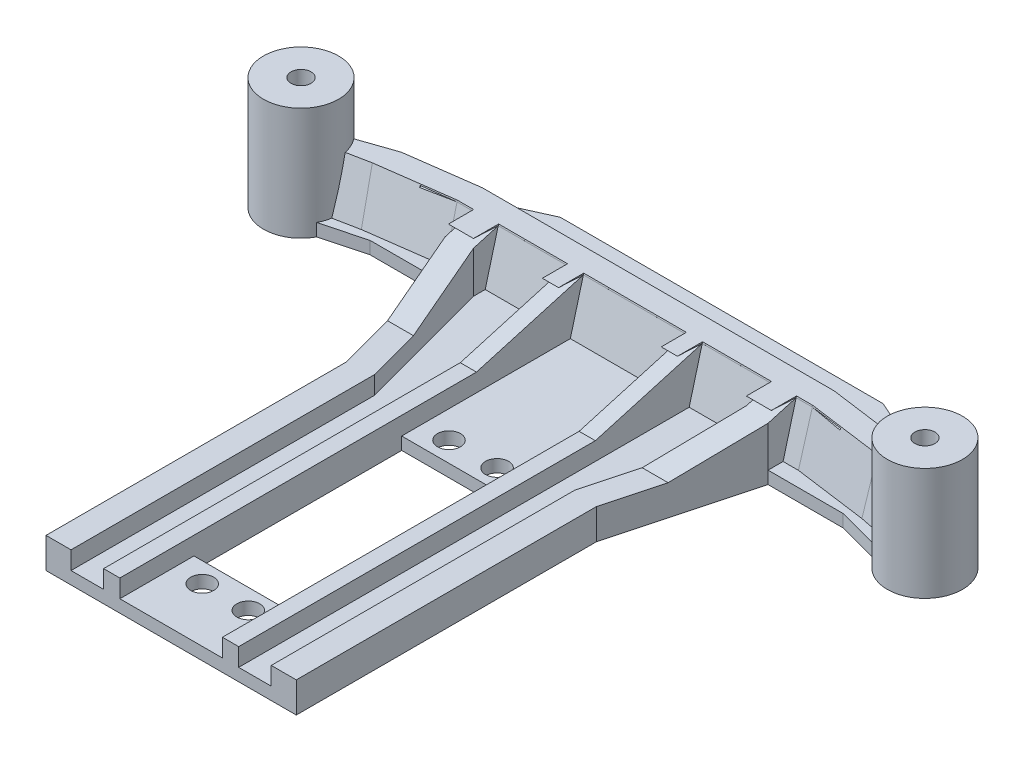
SolidWorks part; units mm, degrees
ref_plane "Front Plane" through (0, 0, 0) normal (0, 0, 1) x (1, 0, 0)
ref_plane "Top Plane" through (0, 0, 0) normal (0, 1, 0) x (1, 0, 0)
ref_plane "Right Plane" through (0, 0, 0) normal (1, 0, 0) x (0, 0, -1)
sketch "Sketch1" plane through (0, 0, 0) normal (0, 1, 0) x (1, 0, 0)
  line L0 (-25, 30) -> (-32.2561, 57)
  line L2 (-25, 30) -> (-25, -30)
  line L3 (-25, -30) -> (25, -30)
  line L4 (25, 30) -> (25, -30)
  line L5 (-25, 30) -> (25, -30) construction
  line L6 (-25, -30) -> (25, 30) construction
  line L7 (-32.2561, 57) -> (-47.2561, 57)
  line L8 (-47.2561, 57) -> (-66, 52)
  line L9 (-66, 52) -> (-66, 62)
  line L10 (-66, 62) -> (-50, 72)
  line L11 (-50, 72) -> (-32.2561, 80)
  line L12 (-32.2561, 80) -> (32.2561, 80)
  line L13 (32.2561, 80) -> (50, 72)
  line L14 (50, 72) -> (66, 62)
  line L15 (66, 62) -> (66, 52)
  line L16 (66, 52) -> (47.2561, 57)
  line L17 (47.2561, 57) -> (32.2561, 57)
  line L18 (32.2561, 57) -> (25, 30)
  line L19 (-32.2561, 57) -> (32.2561, 57) construction
  line L20 (-66, 52) -> (66, 52) construction
  line L21 (-66, 62) -> (66, 62) construction
  line L22 (-50, 72) -> (50, 72) construction
  line L23 (0, 80) -> (0, -30) construction
  line L24 (-25, 30) -> (25, 30) construction
  point P0 (0, 0)
  point P20 (0, 72)
  point P21 (0, 62)
  point P22 (0, 57)
  point P23 (-32.2561, 57)
  dimension "D1" = 50
  dimension "D2" = 60
  dimension "D3" = 50
  dimension "D4" = 27
  dimension "D5" = 15
  dimension "D6" = 15
  dimension "D7" = 5
  dimension "D8" = 5
  dimension "D9" = 10
  dimension "D10" = 100
  dimension "D11" = 132
extrude "Boss-Extrude1" add sketch "Sketch1" along normal blind 2.5
sketch "Sketch2" plane through (0, 2.5, 0) normal (0, 1, 0) x (1, 0, 0)
  line L0 (0, 0) -> (0, 5.5599) construction
  line L1 (-10.25, 26.3099) -> (10.25, 26.3099)
  line L2 (-10.25, 26.3099) -> (-10.25, -15.1901)
  line L3 (-10.25, -15.1901) -> (10.25, -15.1901)
  line L4 (10.25, 26.3099) -> (10.25, -15.1901)
  line L5 (-10.25, 26.3099) -> (10.25, -15.1901) construction
  line L6 (-10.25, -15.1901) -> (10.25, 26.3099) construction
  point P0 (0, 5.5599)
  dimension "D1" = 41.5
  dimension "D2" = 20.5
extrude "Cut-Extrude1" cut sketch "Sketch2" against normal through all
sketch "Sketch8" plane through (0, 2.5, 0) normal (0, 1, 0) x (1, 0, 0)
  line L0 (10.25, 26.3099) -> (-10.25, 26.3099) construction
  line L1 (4.8, 30.3099) -> (-4.8, 30.3099) construction
  line L2 (4.6, -19.1901) -> (-4.6, -19.1901) construction
  line L3 (0, -19.1901) -> (0, 0) construction
  line L4 (-10.25, -15.1901) -> (10.25, -15.1901) construction
  circle A0 centre (-4.8, 30.3099) radius 2.3
  circle A1 centre (4.8, 30.3099) radius 2.3
  circle A2 centre (-4.6, -19.1901) radius 2.3
  circle A3 centre (4.6, -19.1901) radius 2.3
  dimension "D4" = 4.6
  dimension "D5" = 4.6
  dimension "D1" = 4.8
  dimension "D2" = 4.8
  dimension "D3" = 4
  dimension "D6" = 9.2
  dimension "D7" = 4
extrude "Cut-Extrude2" cut sketch "Sketch8" against normal through all
sketch "Sketch9" plane through (0, 2.5, 0) normal (0, 1, 0) x (1, 0, 0)
  line L0 (-65, 62.845) -> (-50, 68)
  line L1 (-50, 68) -> (-35.3199, 70)
  line L2 (-35.3199, 70) -> (35.3199, 70)
  line L3 (35.3199, 70) -> (50, 68)
  line L4 (50, 68) -> (65, 62.845)
  line L5 (65, 62.845) -> (65, 55)
  line L6 (65, 55) -> (50, 58)
  line L7 (50, 58) -> (35.3199, 60)
  line L8 (35.3199, 60) -> (-35.3199, 60)
  line L9 (-35.3199, 60) -> (-50, 58)
  line L10 (-50, 58) -> (-65, 55)
  line L11 (-65, 55) -> (-65, 62.845)
  line L12 (-50, 58) -> (50, 58) construction
  line L13 (-50, 68) -> (50, 68) construction
  line L14 (0, 70) -> (0, 0) construction
  line L15 (-65, 55) -> (65, 55) construction
  line L16 (-35.3199, 70) -> (-35.3199, 60) construction
  line L17 (-50, 68) -> (-50, 58) construction
  line L18 (35.3199, 70) -> (35.3199, 60) construction
  line L19 (50, 68) -> (50, 58) construction
  line L20 (-65, 62.845) -> (65, 62.845) construction
  point P15 (0, 68)
  point P16 (0, 60)
  point P17 (0, 55)
  dimension "D1" = 130
  dimension "D2" = 60
  dimension "D3" = 55
  dimension "D4" = 58
  dimension "D5" = 70
  dimension "D6" = 100
extrude "Boss-Extrude2" add sketch "Sketch9" along normal blind 10 draft 15
sketch "Sketch10" plane through (0, 2.5, 0) normal (0, 1, 0) x (1, 0, 0)
  circle A0 centre (-62.3205, 58.2685) radius 7.5
  circle A1 centre (62.3205, 58.2685) radius 7.5
  dimension "D1" = 15
  dimension "D2" = 15
extrude "Boss-Extrude3" add sketch "Sketch10" along normal blind 20 and the other way blind 2.5
sketch "Sketch11" plane through (0, 22.5, 0) normal (0, 1, 0) x (1, 0, 0)
  circle A0 centre (-62.3205, 58.2685) radius 2
  circle A1 centre (62.3205, 58.2685) radius 2
extrude "Cut-Extrude3" cut sketch "Sketch11" against normal through all
sketch "Sketch12" plane through (0, 2.5, 0) normal (0, 1, 0) x (1, 0, 0)
  line L0 (-25, -30) -> (-25, 30)
  line L1 (-25, 30) -> (-32.2561, 57)
  line L2 (-32.2561, 57) -> (-32.2561, 65.2594)
  line L3 (-32.2561, 65.2594) -> (-27.2561, 65.2594)
  line L4 (-27.2561, 65.2594) -> (-27.2561, 57.6601)
  line L5 (-27.2561, 57.6601) -> (-20, 30.6601)
  line L6 (-20, 30.6601) -> (-20, -30)
  line L7 (-25, -30) -> (25, -30) construction
  line L8 (-20, -30) -> (-25, -30)
  line L9 (-10.25, -15.1901) -> (-10.25, -30)
  line L10 (-10.25, -30) -> (-13.4933, -30)
  line L11 (-13.4933, -30) -> (-13.4933, 64.7299)
  line L12 (-13.4933, 64.7299) -> (-10.25, 64.7299)
  line L13 (-10.25, 64.7299) -> (-10.25, 26.3099)
  line L14 (-10.25, 26.3099) -> (-10.25, -15.1901)
  dimension "D1" = 5
  dimension "D2" = 5
  dimension "D3" = 5
extrude "Boss-Extrude7" add sketch "Sketch12" along normal blind 10
mirror "Mirror2" about plane through (0, 0, 0) normal (1, 0, 0) of "Boss-Extrude7"
sketch "Sketch13" plane through (0, 0, 0) normal (1, 0, 0) x (0, 0, -1)
  line L0 (-30, 6.0913) -> (41.254, 6.0913)
  line L1 (-30, 12.5) -> (-30, 0) construction
  line L2 (41.254, 6.0913) -> (62.6088, 12.2291)
  line L3 (62.6088, 12.2291) -> (-30, 17.29)
  line L4 (-30, 17.29) -> (-30, 6.0913)
  point P4 (64.6251, 12.3046)
  point P7 (62.6088, 12.2291)
  point P8 (41.254, 6.0913)
extrude "Cut-Extrude4" cut sketch "Sketch13" against normal blind 42 and the other way blind 42
